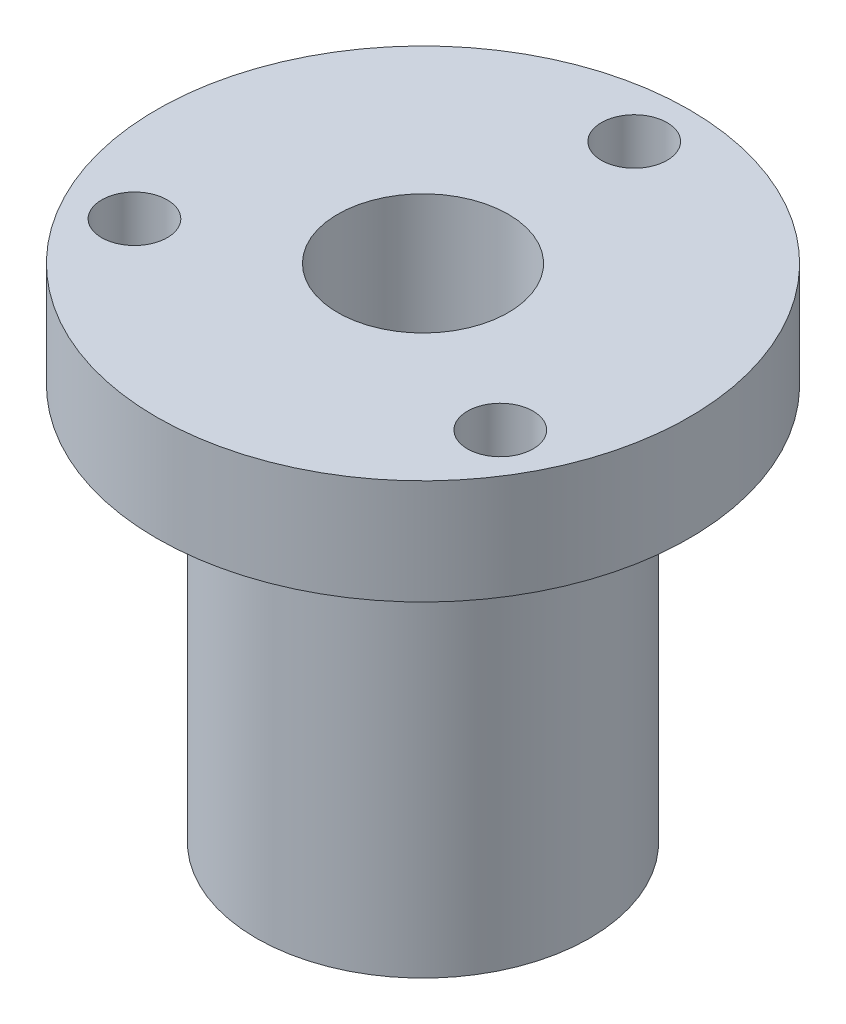
SolidWorks part; units mm, degrees
material "latón"
ref_plane "Alzado" through (0, 0, 0) normal (0, 0, 1) x (1, 0, 0)
ref_plane "Planta" through (0, 0, 0) normal (0, 1, 0) x (1, 0, 0)
ref_plane "Vista lateral" through (0, 0, 0) normal (1, 0, 0) x (0, 0, -1)
sketch "Croquis1" plane through (0, 0, 0) normal (0, 0, 1) x (1, 0, 0)
  line L0 (0, 0) -> (0, 19.1) construction
  line L1 (6.35, 0) -> (6.35, 15.1)
  line L2 (6.35, 15.1) -> (10.15, 15.1)
  line L3 (10.15, 15.1) -> (10.15, 19.1)
  line L4 (10.15, 19.1) -> (3.25, 19.1)
  line L5 (3.25, 19.1) -> (3.25, 0)
  line L6 (3.25, 0) -> (6.35, 0)
  dimension "D1" = 12.7
  dimension "D2" = 20.3
  dimension "D3" = 19.1
  dimension "D4" = 3.1
  dimension "D6" = 4
revolve "Revolución1" add sketch "Croquis1" angle 360 about L0
cosmetic thread "Rosca cosmética1"
sketch "Croquis2" plane through (0, 19.1, 0) normal (0, 1, 0) x (1, 0, 0)
  line L0 (0, 9.3) -> (0, 10.15) construction
  line L1 (6.9715, -4.025) -> (0, 0) construction
  line L2 (0, 0) -> (-6.9715, -4.025) construction
  line L3 (0, 0) -> (0, 8.05) construction
  circle A0 centre (0, 0) radius 8.05 construction
  circle A1 centre (6.9715, -4.025) radius 1.25
  circle A3 centre (0, 8.05) radius 1.25
  circle A4 centre (-6.9715, -4.025) radius 1.25
  circle A7 centre (0, 0) radius 6.35 construction
  circle A8 centre (0, 0) radius 6.35 construction
  circle A9 centre (0, 0) radius 10.15 construction
  dimension "D1" = 2.5
  dimension "D5" = 16.1
  dimension "D2" = 0.85
  dimension "D3" = 120
  dimension "D4" = 120
extrude "Cortar-Extruir1" cut sketch "Croquis2" against normal up to next
cosmetic thread "Rosca de taladro9"
cosmetic thread "Rosca de taladro10"
cosmetic thread "Rosca de taladro11"
hole_wizard "Taladro roscado M31" positions "Croquis3D1" profile "Croquis3" tap size "M3" standard "ISO"
sketch3d "Croquis3D1"
  line L0 (0, 15.1, -8.05) -> (0, 19.1, -8.05) construction
  line L1 (6.9715, 15.1, 4.025) -> (6.9715, 19.1, 4.025) construction
  line L2 (-6.9715, 15.1, 4.025) -> (-6.9715, 19.1, 4.025) construction
  point P0 (0, 15.1, -8.05)
  point P4 (6.9715, 15.1, 4.025)
  point P8 (-6.9715, 15.1, 4.025)
sketch "Croquis3" plane through (0, 15.1, -8.05) normal (1, 0, 0) x (0, 0, -1)
  line L0 (0, 0) -> (0, 9.2511)
  line L1 (0, 9.2511) -> (1.25, 8.5)
  line L2 (1.25, 8.5) -> (1.25, 0)
  line L5 (1.25, 0) -> (0, 0)
  line L10 (0, 9.2511) -> (-1.25, 8.5) construction
  line L11 (0, -6.35) -> (0, 107.95) construction
  dimension "Diámetro de perforador para roscar" = 2.5
  dimension "Profundidad de perforador para roscar" = 8.5
  dimension "Ángulo de perforador" = 118
